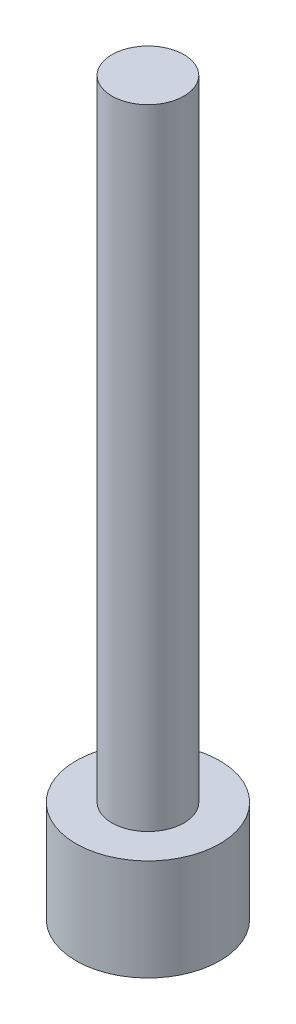
SolidWorks part; units mm, degrees
ref_plane "Спереди" through (0, 0, 0) normal (0, 0, 1) x (1, 0, 0)
ref_plane "Сверху" through (0, 0, 0) normal (0, 1, 0) x (1, 0, 0)
ref_plane "Справа" through (0, 0, 0) normal (1, 0, 0) x (0, 0, -1)
sketch "Эскиз1" plane through (0, 0, 0) normal (1, 0, 0) x (0, 0, -1)
  line L0 (0, 101.7893) -> (0, -44.9948) construction
  line L1 (0, 0) -> (8, 0)
  line L2 (8, 0) -> (8, 11.2811)
  line L3 (8, 11.2811) -> (4, 11.2811)
  line L4 (4, 11.2811) -> (4, 81.3018)
  line L5 (4, 81.3018) -> (0, 81.3018)
  line L7 (0, 81.3018) -> (0, 0)
revolve "Повернуть1" add sketch "Эскиз1" angle 360 about L0
